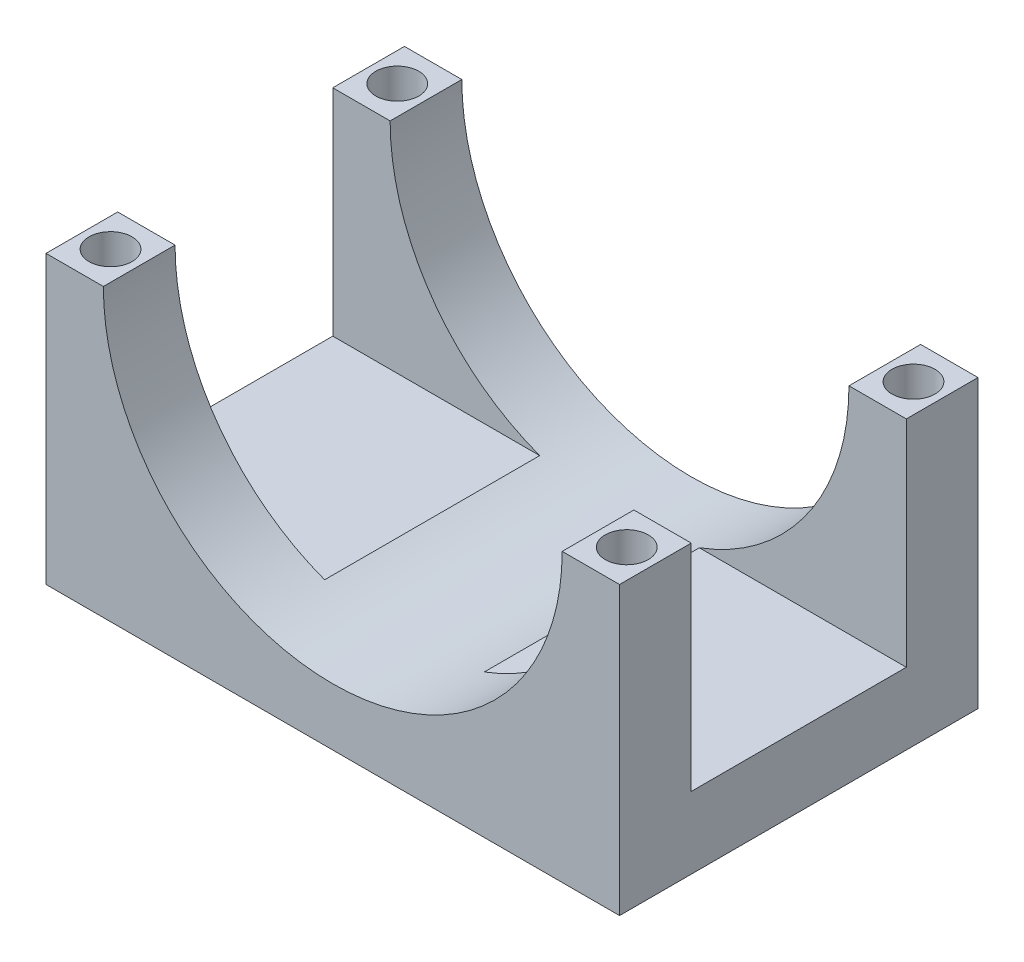
SolidWorks part; units mm, degrees
ref_plane "Alzado" through (0, 0, 0) normal (0, 0, 1) x (1, 0, 0)
ref_plane "Planta" through (0, 0, 0) normal (0, 1, 0) x (1, 0, 0)
ref_plane "Vista lateral" through (0, 0, 0) normal (1, 0, 0) x (0, 0, -1)
sketch "Croquis1" plane through (0, 0, 0) normal (0, 1, 0) x (1, 0, 0)
  line L1 (0, 0) -> (40, 0)
  line L2 (0, 0) -> (0, 25)
  line L3 (0, 25) -> (40, 25)
  line L4 (40, 0) -> (40, 25)
  dimension "D1" = 40
  dimension "D2" = 25
extrude "Saliente-Extruir1" add sketch "Croquis1" along normal blind 20
sketch "Croquis2" plane through (0, 0, 0) normal (0, 0, 1) x (1, 0, 0)
  line L0 (0, 20) -> (40, 20) construction
  circle A0 centre (20, 20) radius 16
  dimension "D1" = 32
extrude "Cortar-Extruir1" cut sketch "Croquis2" against normal through all
sketch "Croquis3" plane through (0, 20, 0) normal (0, 1, 0) x (1, 0, 0)
  line L0 (0, 0) -> (4, 0) construction
  line L3 (40, 25) -> (36, 25) construction
  line L4 (36, 0) -> (40, 0) construction
  line L5 (4, 25) -> (0, 25) construction
  circle A0 centre (2, 2.5) radius 1.5
  circle A1 centre (2, 22.5) radius 1.5
  circle A2 centre (38, 2.5) radius 1.5
  circle A4 centre (38, 22.5) radius 1.5
  dimension "D1" = 3
  dimension "D3" = 3
  dimension "D4" = 3
  dimension "D5" = 3
  dimension "D2" = 2.5
  dimension "D6" = 2.5
  dimension "D7" = 2.5
  dimension "D8" = 2.5
extrude "Cortar-Extruir2" cut sketch "Croquis3" against normal through all
sketch "Croquis4" plane through (40, 0, 0) normal (1, 0, 0) x (0, 0, -1)
  line L0 (5, 20) -> (5, 5)
  line L1 (0, 20) -> (25, 20) construction
  line L2 (5, 5) -> (20, 5)
  line L3 (20, 5) -> (20, 20)
  line L4 (0, 0) -> (25, 0) construction
  line L5 (25, 20) -> (25, 0) construction
  line L6 (0, 20) -> (0, 0) construction
  line L7 (5, 20) -> (20, 20)
  dimension "D1" = 5
  dimension "D2" = 5
  dimension "D3" = 5
extrude "Cortar-Extruir3" cut sketch "Croquis4" against normal through all
